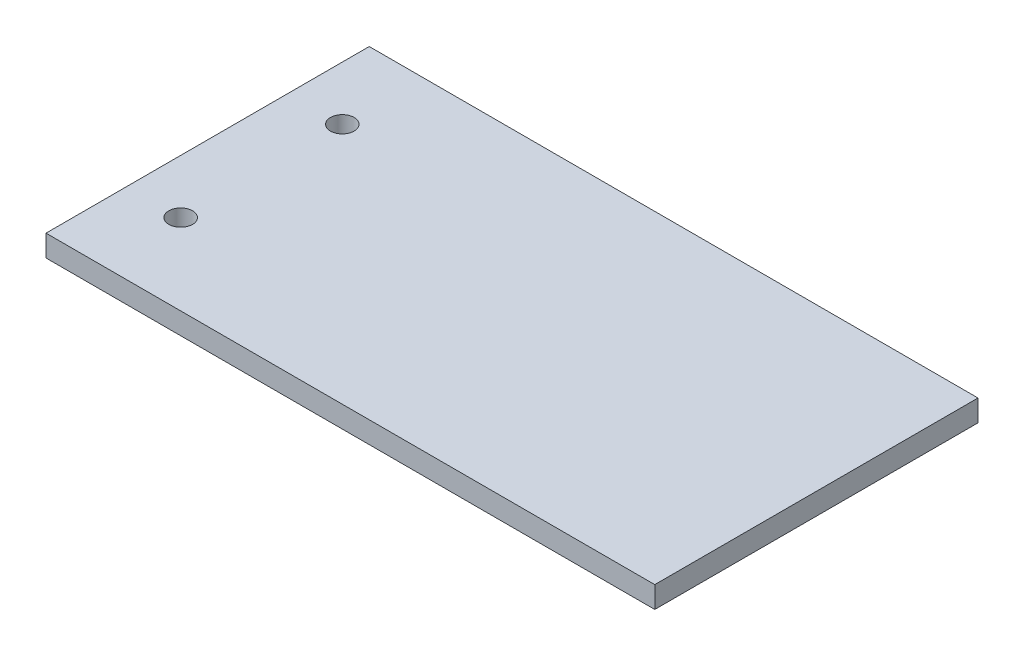
SolidWorks part; units mm, degrees
ref_plane "Front Plane" through (0, 0, 0) normal (0, 0, 1) x (1, 0, 0)
ref_plane "Top Plane" through (0, 0, 0) normal (0, 1, 0) x (1, 0, 0)
ref_plane "Right Plane" through (0, 0, 0) normal (1, 0, 0) x (0, 0, -1)
sketch "Sketch1" plane through (0, 0, 0) normal (0, 1, 0) x (1, 0, 0)
  line L1 (0, 30) -> (113, 30)
  line L2 (0, 30) -> (0, -30)
  line L3 (0, -30) -> (113, -30)
  line L4 (113, 30) -> (113, -30)
  circle A0 centre (10, 15) radius 2.2
  circle A1 centre (10, -15) radius 2.2
extrude "Boss-Extrude1" add sketch "Sketch1" along normal blind 4
